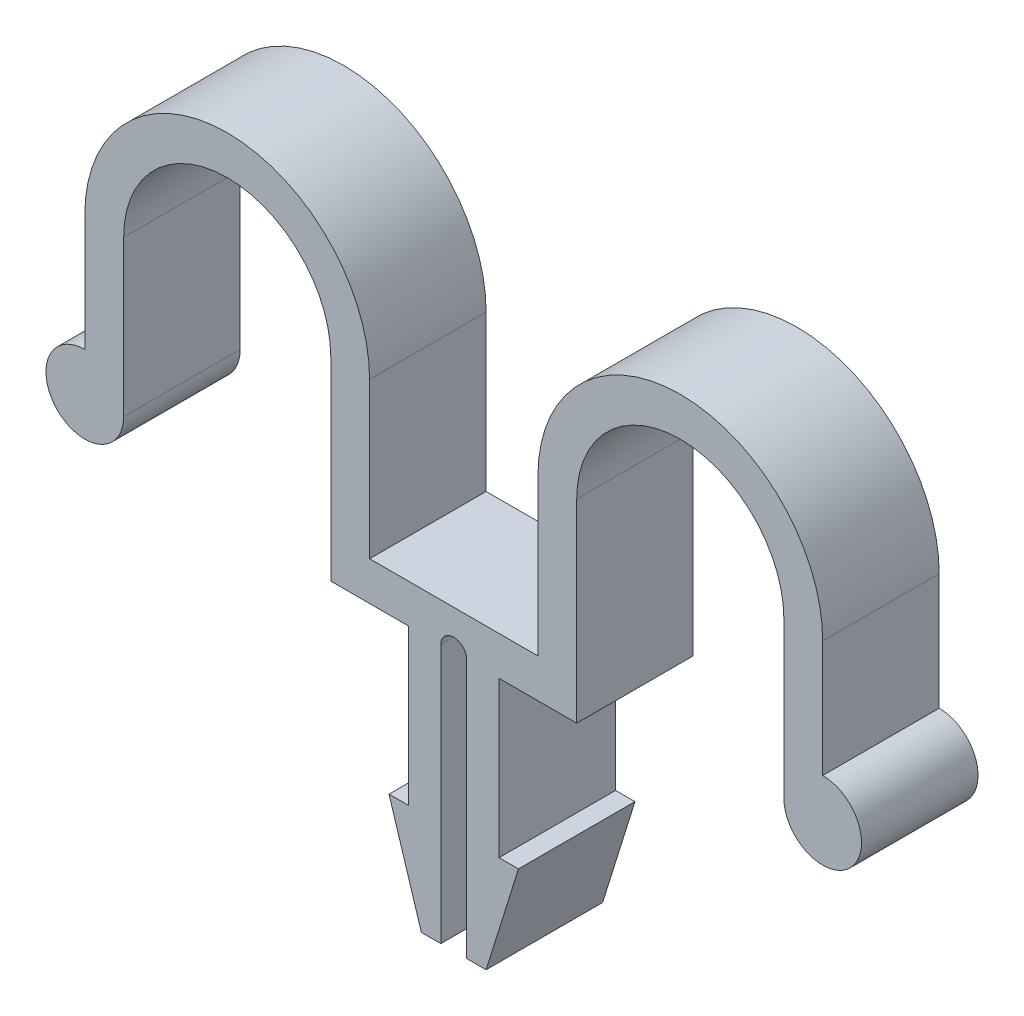
SolidWorks part; units mm, degrees
ref_plane "Ön Düzlem" through (0, 0, 0) normal (0, 0, 1) x (1, 0, 0)
ref_plane "Üst Düzlem" through (0, 0, 0) normal (0, 1, 0) x (1, 0, 0)
ref_plane "Sağ Düzlem" through (0, 0, 0) normal (1, 0, 0) x (0, 0, -1)
sketch "Sketch1" plane through (0, 0, 0) normal (0, 0, 1) x (1, 0, 0)
  line L0 (0, 3) -> (0, 12)
  line L1 (3, 0) -> (3, 12)
  line L2 (3, 3) -> (3, 12) construction
  line L3 (19, 12) -> (19, -3)
  line L4 (22, 12) -> (22, 0)
  line L5 (19, -3) -> (25, -3)
  line L6 (25, -3) -> (25, -15)
  line L7 (25, -15) -> (23.5, -15)
  line L8 (23.5, -15) -> (26, -23)
  line L9 (26, -23) -> (27.5, -23)
  line L10 (22, 0) -> (35, 0)
  line L11 (27.5, -23) -> (27.5, -3)
  line L12 (-5.4683, 12) -> (26, 12) construction
  line L13 (29.5, -23) -> (29.5, -3)
  line L14 (31, -23) -> (29.5, -23)
  line L15 (33.5, -15) -> (31, -23)
  line L16 (32, -15) -> (33.5, -15)
  line L17 (32, -3) -> (32, -15)
  line L18 (38, -3) -> (32, -3)
  line L19 (35, 12) -> (35, 0)
  line L20 (38, 12) -> (38, -3)
  line L21 (54, 0) -> (54, 12)
  line L22 (57, 3) -> (57, 12)
  line L23 (11, 30.9489) -> (11, 3) construction
  line L24 (32.5921, 12) -> (61.2398, 12) construction
  line L25 (46, 26.2853) -> (46, 2.0157) construction
  line L26 (15.8527, -3) -> (41.0084, -3) construction
  line L27 (-4.2673, 0) -> (5.1801, 0) construction
  line L28 (0, 4.117) -> (0, -5.0605) construction
  line L29 (51.9854, 0) -> (62.6205, 0) construction
  line L30 (57, 4.117) -> (57, -6.2481) construction
  line L31 (28.5, 9.3511) -> (28.5, -29.0564) construction
  arc A0 (0, 3) -> (3, 0) centre (0, 0) ccw
  arc A1 (0, 12) -> (22, 12) centre (11, 12) cw
  arc A2 (3, 12) -> (19, 12) centre (11, 12) cw
  arc A3 (27.5, -3) -> (29.5, -3) centre (28.5, -3) cw
  arc A4 (54, 12) -> (38, 12) centre (46, 12) ccw
  arc A5 (57, 12) -> (35, 12) centre (46, 12) ccw
  arc A6 (57, 3) -> (54, 0) centre (57, 0) cw
  point P36 (28.5, 0)
  dimension "D1" = 3
  dimension "D4" = 5
  dimension "D6" = 1
  dimension "D7" = 3
  dimension "D8" = 11
  dimension "D9" = 8
  dimension "D2" = 8
  dimension "D3" = 20
  dimension "D5" = 10
extrude "Boss-Extrude1" add sketch "Sketch1" along normal blind 9
